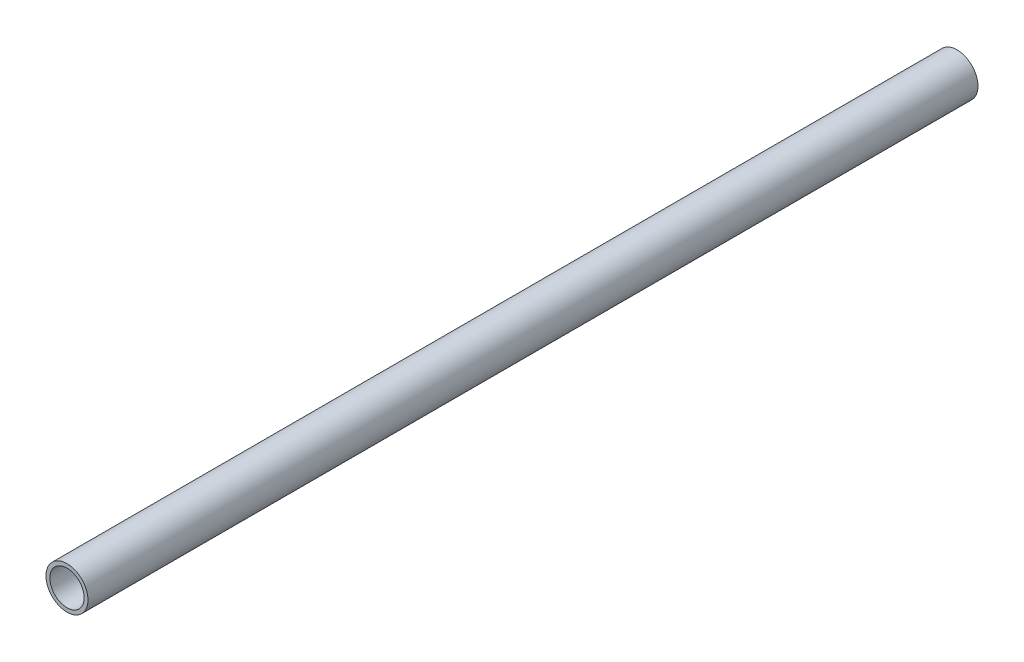
SolidWorks part; units mm, degrees
ref_plane "Front Plane" through (0, 0, 0) normal (0, 0, 1) x (1, 0, 0)
ref_plane "Top Plane" through (0, 0, 0) normal (0, 1, 0) x (1, 0, 0)
ref_plane "Right Plane" through (0, 0, 0) normal (1, 0, 0) x (0, 0, -1)
sketch "Sketch2" plane through (0, 0, 0) normal (0, 0, 1) x (1, 0, 0)
  circle A0 centre (0, 0) radius 3.125
  circle A1 centre (0, 0) radius 3.825
  dimension "D1" = 6.25
  dimension "D2" = 7.65
extrude "Boss-Extrude1" add sketch "Sketch2" along normal mid plane 162
equation "\"D1@Boss-Extrude1\"=100+62"
